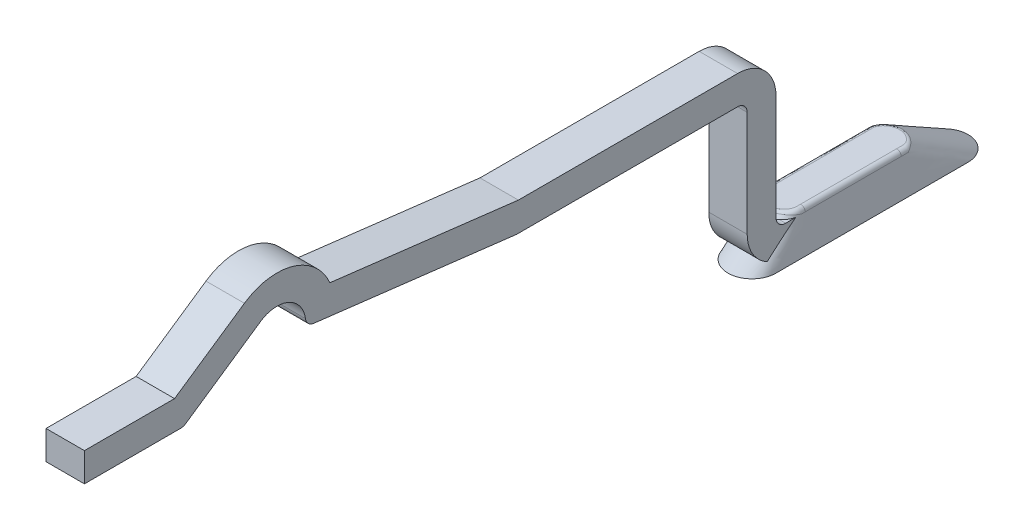
SolidWorks part; units mm, degrees
material "普通碳钢"
ref_plane "Front Plane" through (0, 0, 0) normal (0, 0, 1) x (1, 0, 0)
ref_plane "Top Plane" through (0, 0, 0) normal (0, 1, 0) x (1, 0, 0)
ref_plane "Right Plane" through (0, 0, 0) normal (1, 0, 0) x (0, 0, -1)
ref_plane "Plane1" through (0, -0.05, 0) normal (0, 1, 0) x (1, 0, 0)
sketch "Sketch1" plane through (0, 0, 0) normal (1, 0, 0) x (0, 0, -1)
  line L0 (1.5, 0) -> (0.4, 0)
  line L1 (0.2811, 0) -> (-0.2811, 0) construction
  line L2 (0, 0.4) -> (0, 1.5)
  line L3 (0, 0.2811) -> (0, -0.2811) construction
  line L4 (-0.1, 1.6) -> (-2.4, 1.6)
  line L5 (-2.4, 1.6) -> (-4.5119, 1.8538)
  line L6 (-5.0654, 2.1479) -> (-5.8437, 1.6174)
  line L7 (-5.9, 1.6) -> (-6.9, 1.6)
  arc A0 (0.4, 0) -> (0, 0.4) centre (0.4, 0.4) cw
  arc A1 (0, 1.5) -> (-0.1, 1.6) centre (-0.1, 1.5) ccw
  arc A2 (-4.5991, 1.9398) -> (-5.0654, 2.1479) centre (-4.8965, 1.9) ccw
  arc A3 (-4.5119, 1.8538) -> (-4.5991, 1.9398) centre (-4.5, 1.9531) cw
  arc A4 (-5.8437, 1.6174) -> (-5.9, 1.6) centre (-5.9, 1.7) cw
  point P11 (0, 0)
  point P14 (0, 1.6)
  dimension "D3" = 0.4
  dimension "D4" = 0.1
  dimension "D6" = 0.1
  dimension "D7" = 0.1
  dimension "D9" = 0.3
  dimension "D1" = 1.6
  dimension "D2" = 1.5
  dimension "D5" = 2.4
  dimension "D8" = 5.9
  dimension "D10" = 1
  dimension "D11" = 4.5
  dimension "D12" = 0
  dimension "D13" = 0.3
extrude "Extrude-Thin1" add sketch "Sketch1" along normal mid plane 0.4 thin
sketch "Sketch2" plane through (0, -0.05, 0) normal (0, 1, 0) x (1, 0, 0)
  line L0 (0, 2.25) -> (0, 0.25) construction
  line L1 (0, -1.7919) -> (0, 1.7919) construction
  line L2 (0.25, 2.25) -> (0.25, 0.25)
  line L3 (-0.25, 2.25) -> (-0.25, 0.25)
  line L4 (-0.2811, 0) -> (0.2811, 0) construction
  arc A0 (0.25, 2.25) -> (-0.25, 2.25) centre (0, 2.25) ccw
  arc A1 (-0.25, 0.25) -> (0.25, 0.25) centre (0, 0.25) ccw
  point P5 (0, 1.25)
  dimension "D1" = 0.5
  dimension "D2" = 1.25
  dimension "D3" = 2
ref_plane "Plane2" through (0, 0.35, 0) normal (0, 1, 0) x (1, 0, 0)
sketch "Sketch3" plane through (0, 0.35, 0) normal (0, 1, 0) x (1, 0, 0)
  line L0 (0, 1.6) -> (0, 0.6) construction
  line L1 (0, 2.25) -> (0, 0.25) construction
  line L2 (0.2, 1.6) -> (0.2, 0.6)
  line L3 (-0.2, 1.6) -> (-0.2, 0.6)
  line L4 (-0.2811, 0) -> (0.2811, 0) construction
  arc A0 (0.2, 1.6) -> (-0.2, 1.6) centre (0, 1.6) ccw
  arc A1 (-0.2, 0.6) -> (0.2, 0.6) centre (0, 0.6) ccw
  point P4 (0, 1.1)
  dimension "D2" = 0.2
  dimension "D1" = 1
  dimension "D3" = 1.1
loft "Loft1" add profiles "Sketch3", "Sketch2"
fillet "Fillet2" radius 0.05 4 edges
